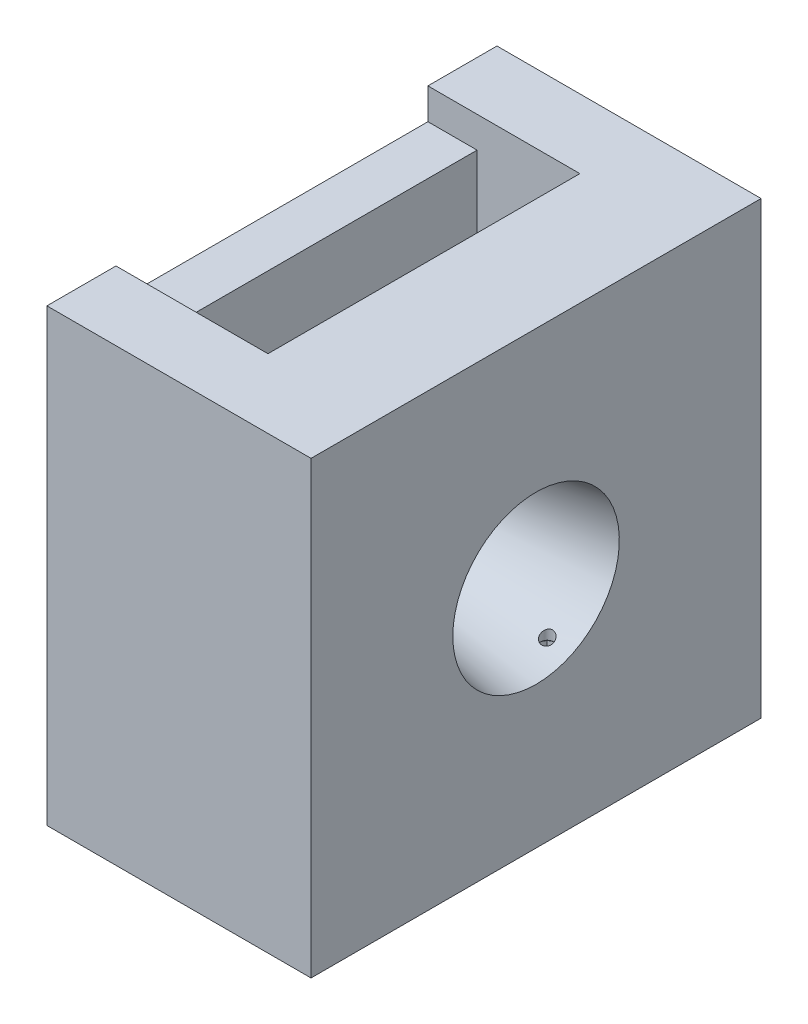
SolidWorks part; units mm, degrees
ref_plane "Plano frontal" through (0, 0, 0) normal (0, 0, 1) x (1, 0, 0)
ref_plane "Plano superior" through (0, 0, 0) normal (0, 1, 0) x (1, 0, 0)
ref_plane "Plano direito" through (0, 0, 0) normal (1, 0, 0) x (0, 0, -1)
sketch "Esboço1" plane through (0, 0, 0) normal (1, 0, 0) x (0, 0, -1)
  line L1 (-14500, -14500) -> (14500, -14500)
  line L2 (-14500, -14500) -> (-14500, 14500)
  line L3 (-14500, 14500) -> (14500, 14500)
  line L4 (14500, -14500) -> (14500, 14500)
  line L5 (-14500, -14500) -> (14500, 14500) construction
  line L6 (-14500, 14500) -> (14500, -14500) construction
  point P0 (0, 0)
  dimension "D1" = 29000
extrude "Ressalto-extrusão1" add sketch "Esboço1" along normal blind 10050 and the other way blind 6970
sketch "Esboço2" plane through (0, 0, 0) normal (0, 0, 1) x (1, 0, 0)
  line L0 (0, 0) -> (0, 14500) construction
  line L3 (-6970, 14500) -> (10050, 14500) construction
  line L4 (0, 0) -> (10050, 0) construction
  line L5 (10050, 14500) -> (10050, -14500) construction
  line L6 (2824, 4113) -> (10050, 5365)
  line L7 (2824, 4113) -> (2824, 0)
  line L8 (2824, 0) -> (10050, 0)
  line L9 (10050, 0) -> (10050, 5365)
  line L10 (-3800, 5521.5) -> (-6970, 7639)
  line L11 (-6970, 14500) -> (-6970, -14500) construction
  line L12 (-3800, 5521.5) -> (-3800, 0)
  line L13 (-3800, 0) -> (-6970, 0)
  line L14 (-6970, 0) -> (-6970, 7639)
  dimension "D1" = 10730
  dimension "D2" = 8226
  dimension "D3" = 7226
  dimension "D4" = 3800
  dimension "D5" = 11043
  dimension "D6" = 7639
revolve "Corte-Revolução1" cut sketch "Esboço2" angle 360 about L4
sketch "Esboço3" plane through (0, 0, 0) normal (0, 0, 1) x (1, 0, 0)
  line L0 (-3800, -9164) -> (-3800, 12500)
  line L1 (-3800, 12500) -> (-6970, 12500)
  line L2 (-6970, 14500) -> (-6970, -14500) construction
  line L3 (-6970, 12500) -> (-6970, 14500)
  line L4 (-6970, 14500) -> (2824, 14500)
  line L5 (-6970, 14500) -> (10050, 14500) construction
  line L6 (2824, 14500) -> (2824, -9164)
  line L10 (2824, -9164) -> (9370, -9164)
  line L12 (-3800, -9164) -> (-6970, -9164)
  line L13 (-6970, -9164) -> (-6970, -11164)
  line L14 (-6970, -11164) -> (9370, -11164)
  line L15 (9370, -11164) -> (9370, -9164)
  line L16 (2824, -4113) -> (10050, -5365) construction
  line L17 (10050, 14500) -> (10050, -14500) construction
  point P17 (2824, -4113)
  dimension "D1" = 2000
  dimension "D2" = 5051
  dimension "D3" = 680
  dimension "D4" = 2000
extrude "Corte-extrusão1" cut sketch "Esboço3" against normal blind 10050 and the other way blind 10050
sketch "Esboço4" plane through (0, -11164, 0) normal (0, 1, 0) x (1, 0, 0)
  line L1 (7770, 3000) -> (9370, 3000)
  line L2 (7770, 3000) -> (7770, 1400)
  line L3 (7770, 1400) -> (9370, 1400)
  line L4 (9370, 3000) -> (9370, 1400)
  circle A0 centre (8570, 2200) radius 800 construction
  dimension "D1" = 7770
  dimension "D2" = 1600
  dimension "D3" = 3000
extrude "Corte-extrusão2" cut sketch "Esboço4" along normal blind 6050
sketch "Esboço5" plane through (0, -5114, 0) normal (0, -1, 0) x (-1, 0, 0)
  line L0 (-9370, 1400) -> (-7770, 1400) construction
  line L1 (-7770, 1400) -> (-7770, 3000) construction
  circle A0 centre (-8570, 2200) radius 400
  point P4 (-8570, 1400)
  point P7 (-7770, 2200)
  dimension "D1" = 800
extrude "Corte-extrusão3" cut sketch "Esboço5" against normal up to next
sketch "Esboço6" plane through (0, 14500, 0) normal (0, 1, 0) x (1, 0, 0)
  line L0 (7050, 0) -> (-6970, 0)
  line L1 (-6970, -10050) -> (-6970, 10050) construction
  line L2 (-6970, 0) -> (-6970, -14500)
  line L3 (-6970, -14500) -> (10050, -14500)
  line L4 (10050, -14500) -> (10050, 2200)
  line L5 (10050, 14500) -> (10050, -14500) construction
  line L6 (10050, 2200) -> (7050, 2200)
  line L7 (7050, 2200) -> (7050, 0)
  dimension "D1" = 16700
  dimension "D2" = 3000
extrude "Corte_Auxiliar" [suppressed] cut sketch "Esboço6" against normal through all
sketch "Esboço8" plane through (0, -5114, 0) normal (0, -1, 0) x (1, 0, 0)
  circle A0 centre (8570, -2200) radius 495
  dimension "D1" = 990
extrude "Corte-extrusão4" cut sketch "Esboço8" against normal blind 90
